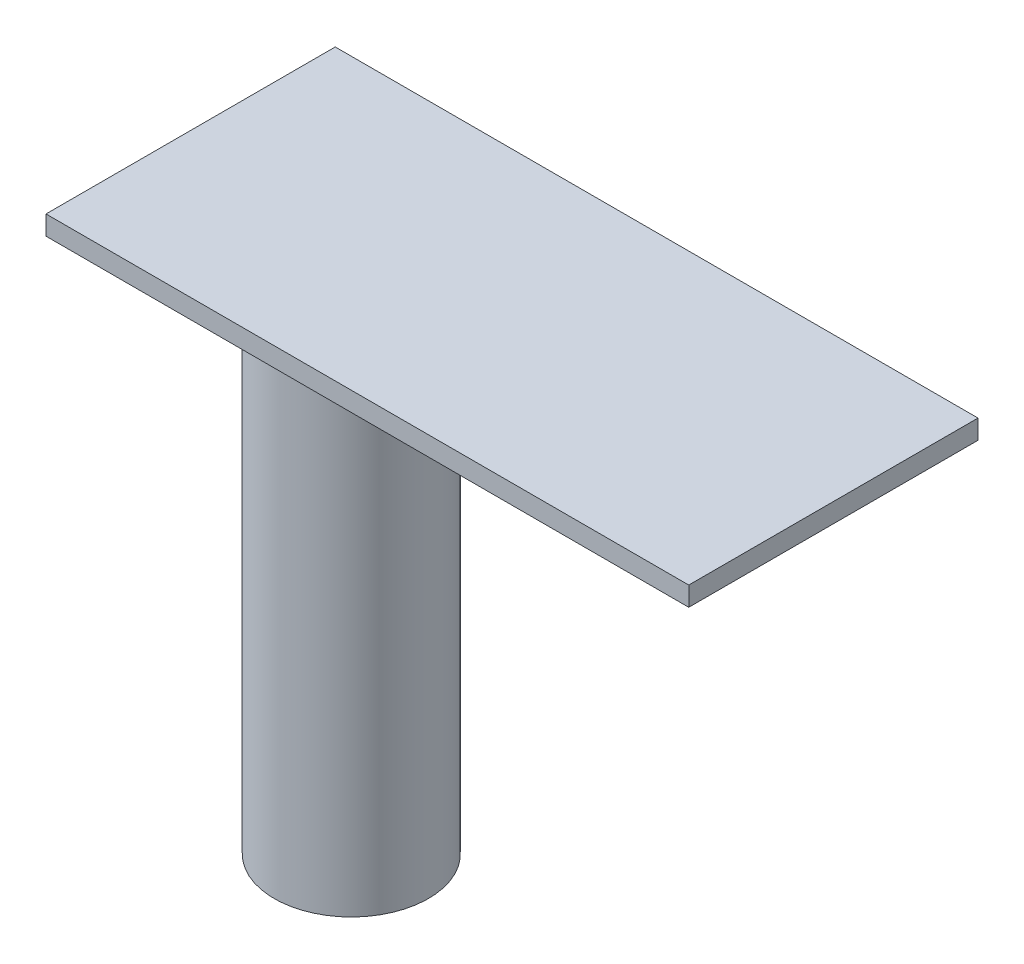
SolidWorks part; units mm, degrees
ref_plane "Спереди" through (0, 0, 0) normal (0, 0, 1) x (1, 0, 0)
ref_plane "Сверху" through (0, 0, 0) normal (0, 1, 0) x (1, 0, 0)
ref_plane "Справа" through (0, 0, 0) normal (1, 0, 0) x (0, 0, -1)
sketch "Эскиз1" plane through (0, 0, 0) normal (0, 1, 0) x (1, 0, 0)
  line L1 (0, 0) -> (100, 0)
  line L2 (0, 0) -> (0, 45)
  line L3 (0, 45) -> (100, 45)
  line L4 (100, 0) -> (100, 45)
extrude "Бобышка-Вытянуть1" add sketch "Эскиз1" along normal blind 3
sketch "Эскиз2" plane through (0, 0, 0) normal (0, -1, 0) x (1, 0, 0)
  circle A0 centre (25, -22.5) radius 12
extrude "Бобышка-Вытянуть2" add sketch "Эскиз2" along normal blind 82
